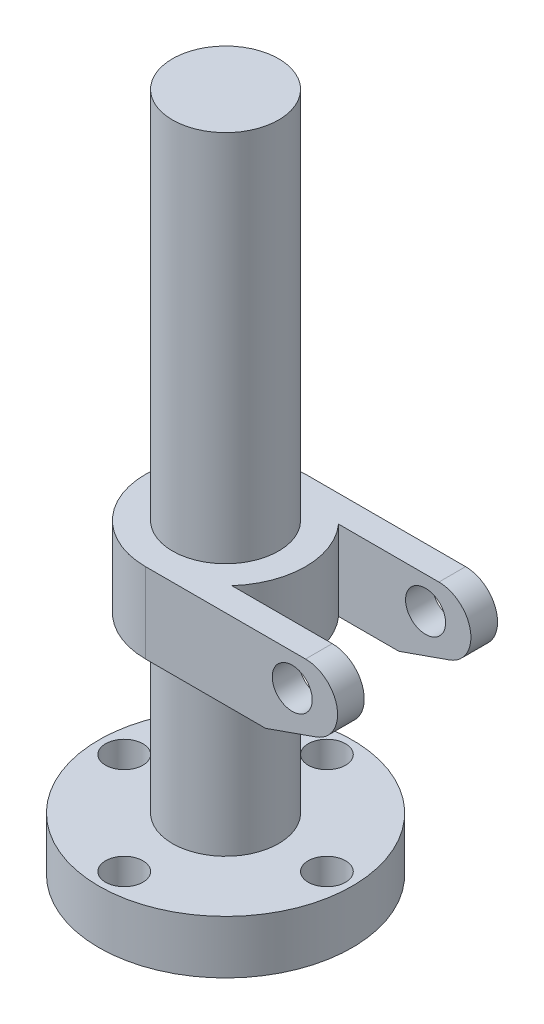
SolidWorks part; units mm, degrees
ref_plane "Front Plane" through (0, 0, 0) normal (0, 0, 1) x (1, 0, 0)
ref_plane "Top Plane" through (0, 0, 0) normal (0, 1, 0) x (1, 0, 0)
ref_plane "Right Plane" through (0, 0, 0) normal (1, 0, 0) x (0, 0, -1)
sketch "Sketch2" plane through (0, 0, 0) normal (0, 0, 1) x (1, 0, 0)
  line L0 (0, 0) -> (0, 157.8223) construction
  line L1 (0, 0) -> (-47.5, 0)
  line L2 (-47.5, 0) -> (-47.5, 20)
  line L3 (-47.5, 20) -> (-19.9, 20)
  line L4 (-19.9, 20) -> (-19.9, 85)
  line L5 (-19.9, 85) -> (-30, 85)
  line L6 (-30, 85) -> (-30, 115)
  line L7 (-30, 115) -> (-19.9, 115)
  line L8 (-19.9, 115) -> (-19.9, 255)
  line L9 (-19.9, 255) -> (0, 255)
  line L10 (0, 255) -> (0, 0)
  line L11 (-20, 0) -> (-20, 15)
  line L12 (-20, 15) -> (0, 15)
  dimension "D1" = 47.5
  dimension "D2" = 20
  dimension "D3" = 65
  dimension "D4" = 39.8
  dimension "D5" = 30
  dimension "D6" = 140
  dimension "D7" = 39.8
  dimension "D8" = 60
  dimension "D9" = 20
  dimension "D10" = 15
revolve "Revolve1" add sketch "Sketch2" angle 360 about L10
sketch "Sketch3" plane through (0, 0, 0) normal (0, 0, 1) x (1, 0, 0)
  line L0 (0, 115) -> (60, 115)
  line L1 (30, 115) -> (-30, 115) construction
  line L2 (63.9835, 91.6805) -> (45, 85)
  line L3 (45, 85) -> (30, 85)
  line L4 (30, 85) -> (0, 85)
  line L5 (-19.9, 85) -> (19.9, 85) construction
  line L6 (0, 85) -> (0, 115)
  arc A0 (60, 115) -> (63.9835, 91.6805) centre (60, 103) cw
  circle A1 centre (55, 103) radius 7.5
  dimension "D1" = 12
  dimension "D3" = 15
  dimension "D5" = 12
  dimension "D2" = 60
  dimension "D4" = 55
  dimension "D6" = 45
extrude "Boss-Extrude1" add sketch "Sketch3" along normal through all and the other way through all
sketch "Sketch4" plane through (0, 115, 0) normal (0, 1, 0) x (1, 0, 0)
  line L0 (0, -30) -> (80.5114, -30)
  line L1 (80.5114, -30) -> (80.5114, 30)
  line L2 (80.5114, 30) -> (0, 30)
  line L3 (30, 0) -> (80.5114, 0) construction
  line L4 (22.3607, 20) -> (85.4786, 20)
  line L5 (0, 47.5) -> (0, 30)
  line L6 (0, -30) -> (0, -47.5)
  line L7 (0, -47.5) -> (60, -47.5)
  line L8 (60, -47.5) -> (60, 47.5)
  line L9 (60, 47.5) -> (0, 47.5)
  line L10 (0, 47.5) -> (0, 30)
  line L11 (0, -30) -> (0, -47.5)
  line L12 (0, -47.5) -> (60, -47.5)
  line L13 (60, -47.5) -> (60, 47.5)
  line L14 (60, 47.5) -> (0, 47.5)
  line L15 (22.3607, -20) -> (85.4786, -20)
  line L16 (60, -47.5) -> (72, -47.5)
  line L17 (72, -47.5) -> (72, 47.5)
  line L18 (72, 47.5) -> (60, 47.5)
  circle A0 centre (0, 0) radius 30
  arc A1 (0, 30) -> (0, -30) centre (0, 0) ccw
  arc A2 (0, 30) -> (0, -30) centre (0, 0) ccw
  line M11 (0, 47.5) -> (0, 30)
  line M13 (0, -30) -> (0, -47.5)
  line M14 (0, -47.5) -> (60, -47.5)
  line M15 (60, -47.5) -> (60, 47.5)
  line M16 (60, 47.5) -> (0, 47.5)
  dimension "D2" = 10
  dimension "D1" = 0
extrude "Cut-Extrude1" cut sketch "Sketch4" against normal up to next contours L0 M13 M14 M15 | L16 L17 L0 M15 | L3 A0 L15 L13 | L3 L13 L15 L17 | A0 L3 L4 M15 | L3 L17 L4 M15 | L2 M15 M16 M11 | L17 L18 L2 M15
sketch "Sketch5" plane through (0, 20, 0) normal (0, 1, 0) x (1, 0, 0)
  circle A0 centre (0, 0) radius 38 construction
  point P4 (0, 38)
  point P6 (-38, 0)
  point P8 (0, -38)
  point P10 (38, 0)
  dimension "D1" = 76
hole_wizard "CBORE for M20 Hex Head Bolt1" positions "Sketch5" profile "Sketch7" counterbore size "M20" standard "ISO" end condition through all
sketch "Sketch7" plane through (38, 20, 0) normal (1, 0, 0) x (0, 0, 1)
  line L0 (0, 0) -> (0, 20)
  line L1 (0, 20) -> (5, 20)
  line L3 (5, 20) -> (5, 10)
  line L4 (5, 10) -> (7, 10)
  line L5 (7, 10) -> (7, 0)
  line L7 (7, 0) -> (0, 0)
  line L11 (0, -6.35) -> (0, 107.95) construction
  dimension "Thru Hole Dia." = 10
  dimension "Thru Hole Depth" = 20
  dimension "C'Bore Dia." = 14
  dimension "C'Bore Depth" = 10
